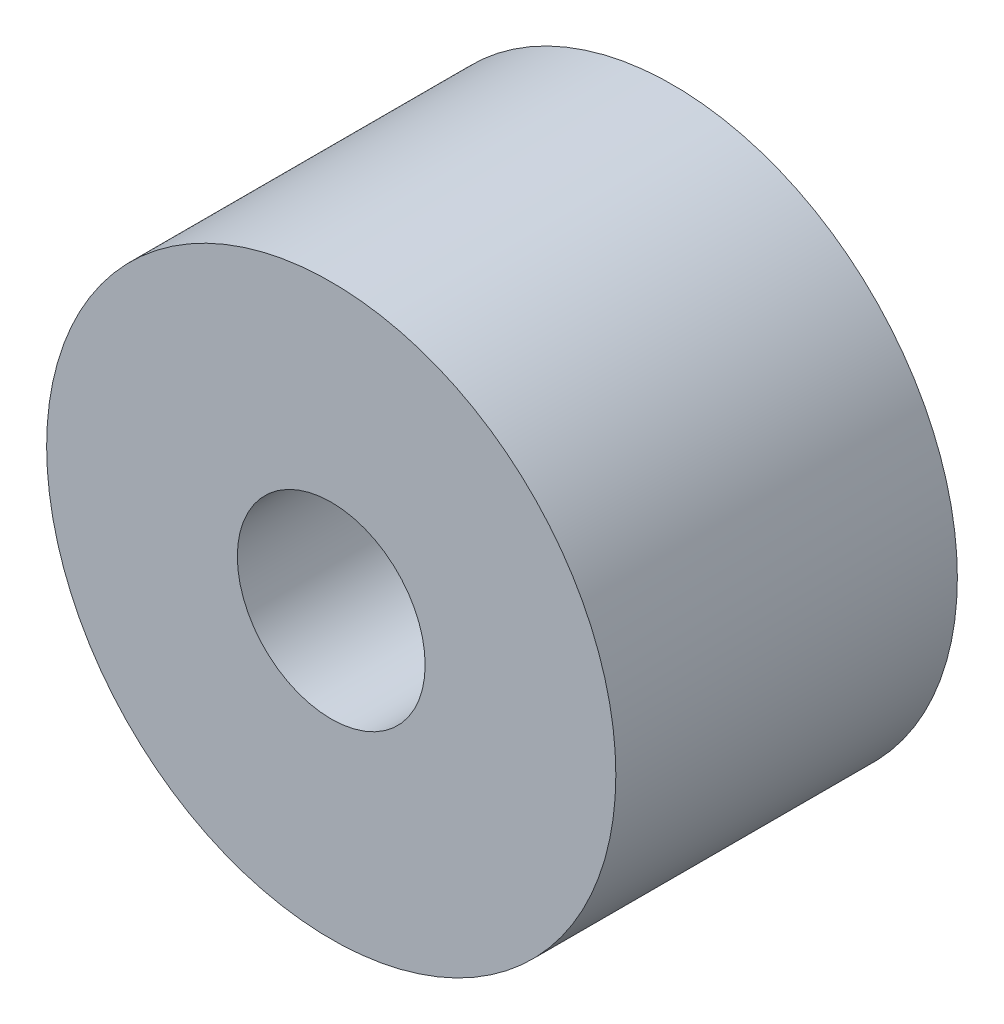
SolidWorks part; units mm, degrees
ref_plane "正面" through (0, 0, 0) normal (0, 0, 1) x (1, 0, 0)
ref_plane "平面" through (0, 0, 0) normal (0, 1, 0) x (1, 0, 0)
ref_plane "右側面" through (0, 0, 0) normal (1, 0, 0) x (0, 0, -1)
sketch "ｽｹｯﾁ1" plane through (0, 0, 0) normal (0, 0, 1) x (1, 0, 0)
  line L0 (-40.4809, 47.4644) -> (-19.4119, 52.6725)
  line L1 (-19.4119, 52.6725) -> (-14.914, 47.4644)
  line L2 (-14.914, 47.4644) -> (-13.1226, 40.2175)
  line L3 (-13.1226, 40.2175) -> (-17.1629, 36.7281)
  line L4 (-17.1629, 36.7281) -> (-17.1629, 28.526)
  line L5 (-17.1629, 28.526) -> (-59.8927, 30.4198)
  line L6 (-59.8927, 30.4198) -> (-61.4521, 36.7281)
  line L7 (-61.4521, 36.7281) -> (-59.8927, 43.8409)
  line L8 (-59.8927, 43.8409) -> (-55.6603, 63.1468)
  line L9 (-55.6603, 63.1468) -> (-57.7765, 63.1468)
  line L10 (-57.7765, 63.1468) -> (-57.7765, 69.4803)
  line L11 (-57.7765, 69.4803) -> (-60.6724, 72.8334)
  line L12 (-60.6724, 72.8334) -> (-67.0927, 74.241)
  line L13 (-67.0927, 74.241) -> (-71.2558, 74.241)
  line L14 (-71.2558, 74.241) -> (-74.357, 74.9208)
  line L15 (-74.357, 74.9208) -> (-67.0927, 78.476)
  line L16 (-67.0927, 78.476) -> (-60.6724, 78.476)
  line L17 (-60.6724, 78.476) -> (-55.6603, 74.241)
  line L18 (-55.6603, 74.241) -> (-47.0998, 74.241)
  line L19 (-47.0998, 74.241) -> (-41.4656, 69.4803)
  line L20 (-41.4656, 69.4803) -> (-40.4809, 53.4938)
  line L21 (-40.4809, 53.4938) -> (-40.4809, 47.4644)
  line L22 (103.0358, 67.5865) -> (103.0358, 78.476)
  line L23 (103.0358, 78.476) -> (111.9152, 78.476)
  line L24 (111.9152, 78.476) -> (111.9152, 67.5865)
  line L25 (111.9152, 67.5865) -> (122.8047, 67.5865)
  line L26 (122.8047, 67.5865) -> (122.8047, 58.7071)
  line L27 (122.8047, 58.7071) -> (111.9152, 58.7071)
  line L28 (111.9152, 58.7071) -> (111.9152, 47.8175)
  line L29 (111.9152, 47.8175) -> (103.0358, 47.8175)
  line L30 (103.0358, 47.8175) -> (103.0358, 58.7071)
  line L31 (103.0358, 58.7071) -> (92.1462, 58.7071)
  line L32 (92.1462, 58.7071) -> (92.1462, 67.5865)
  line L33 (92.1462, 67.5865) -> (103.0358, 67.5865)
  line L34 (41.6645, 50.0684) -> (33.8524, 36.7281)
  line L35 (33.8524, 36.7281) -> (30.8018, 38.5145)
  line L36 (30.8018, 38.5145) -> (25.686, 29.7785)
  line L37 (25.686, 29.7785) -> (20.5955, 28.526)
  line L38 (20.5955, 28.526) -> (17.9766, 24.0538)
  line L39 (17.9766, 24.0538) -> (14.8342, 18.6876)
  line L40 (14.8342, 18.6876) -> (14.8342, 13.612)
  line L41 (14.8342, 13.612) -> (17.9766, 5.5632)
  line L42 (17.9766, 5.5632) -> (21.1614, -2.5939)
  line L43 (21.1614, -2.5939) -> (19.569, -10.2978)
  line L44 (19.569, -10.2978) -> (16.4054, -15.7001)
  line L45 (16.4054, -15.7001) -> (10.482, -18.0127)
  line L46 (10.482, -18.0127) -> (-0.7783, -22.409)
  line L47 (-0.7783, -22.409) -> (-11.1263, -22.409)
  line L48 (-11.1263, -22.409) -> (-24.8567, -18.0127)
  line L49 (-24.8567, -18.0127) -> (-29.5913, -10.2978)
  line L50 (-29.5913, -10.2978) -> (-32.1251, 0)
  line L51 (-32.1251, 0) -> (-108.9262, -34.7071)
  line L52 (-108.9262, -34.7071) -> (-108.9262, -38.2319)
  line L53 (-108.9262, -38.2319) -> (-103.9245, -38.2319)
  line L54 (-103.9245, -38.2319) -> (-102.0442, -41.2959)
  line L55 (-102.0442, -41.2959) -> (-97.7591, -42.668)
  line L56 (-97.7591, -42.668) -> (-95.736, -50.8902)
  line L57 (-95.736, -50.8902) -> (-92.0846, -56.84)
  line L58 (-92.0846, -56.84) -> (-84.2874, -59.3366)
  line L59 (-84.2874, -59.3366) -> (-74.357, -59.3366)
  line L60 (-74.357, -59.3366) -> (-30.8582, -39.6791)
  line L61 (-30.8582, -39.6791) -> (-27.224, -38.0368)
  line L62 (-27.224, -38.0368) -> (-22.8371, -35.3446)
  line L63 (-22.8371, -35.3446) -> (-11.1263, -35.3446)
  line L64 (-11.1263, -35.3446) -> (-0.7783, -35.3446)
  line L65 (-0.7783, -35.3446) -> (10.482, -30.256)
  line L66 (10.482, -30.256) -> (21.7814, -23.3216)
  line L67 (21.7814, -23.3216) -> (30.8018, -12.9989)
  line L68 (30.8018, -12.9989) -> (35.969, -4.1751)
  line L69 (35.969, -4.1751) -> (40.5416, 3.6333)
  line L70 (40.5416, 3.6333) -> (40.5416, 9.5876)
  line L71 (40.5416, 9.5876) -> (45.1164, 17.3997)
  line L72 (45.1164, 17.3997) -> (47.4419, 21.3707)
  line L73 (47.4419, 21.3707) -> (45.1164, 30.8218)
  line L74 (45.1164, 30.8218) -> (41.6645, 33.8381)
  line L75 (41.6645, 33.8381) -> (49.8508, 47.8175)
  line L76 (49.8508, 47.8175) -> (41.6645, 50.0684)
  line L77 (77.2935, 67.6446) -> (77.2935, 32.33)
  line L78 (77.2935, 32.33) -> (77.2935, 28.526)
  line L79 (77.2935, 28.526) -> (82.4095, 27.1193)
  line L80 (82.4095, 27.1193) -> (87.6627, 25.6749)
  line L81 (87.6627, 25.6749) -> (92.1462, 25.6749)
  line L82 (92.1462, 25.6749) -> (120.0222, 21.3707)
  line L83 (120.0222, 21.3707) -> (127.0357, 25.6749)
  line L84 (127.0357, 25.6749) -> (131.2042, 52.6725)
  line L85 (122.8047, 58.7071) -> (131.2042, 58.7071)
  line L86 (131.2042, 58.7071) -> (131.2042, 52.6725)
  line L87 (120.0222, 58.7071) -> (120.0222, 55.1166)
  line L88 (120.0222, 55.1166) -> (120.0222, 43.3983)
  line L89 (120.0222, 43.3983) -> (90.3217, 43.9227)
  line L90 (90.3217, 43.9227) -> (87.52, 48.488)
  line L91 (87.52, 48.488) -> (90.3217, 55.7115)
  line L92 (90.3217, 55.7115) -> (85.0361, 57.7616)
  line L93 (85.0361, 57.7616) -> (85.0361, 67.6446)
  line L94 (85.0361, 67.6446) -> (77.2935, 67.6446)
  line L95 (-17.1629, 67.6446) -> (-17.1629, 60.6019)
  line L96 (-17.1629, 60.6019) -> (19.2861, 54.9741)
  line L97 (19.2861, 54.9741) -> (19.2861, 43.3983)
  line L98 (19.2861, 43.3983) -> (28.2439, 42.0152)
  line L99 (28.2439, 42.0152) -> (33.2702, 54.9741)
  line L100 (33.2702, 54.9741) -> (47.4419, 54.9741)
  line L101 (47.4419, 54.9741) -> (49.8508, 40.8278)
  line L102 (49.8508, 40.8278) -> (61.8287, 38.9784)
  line L103 (61.8287, 38.9784) -> (77.2935, 49.9873)
  line L104 (77.2935, 49.9873) -> (77.2935, 74.241)
  line L105 (77.2935, 74.241) -> (52.7136, 74.241)
  line L106 (52.7136, 74.241) -> (49.8508, 74.241)
  line L107 (49.8508, 74.241) -> (10.482, 74.9361)
  line L108 (10.482, 74.9361) -> (-11.1263, 69.6193)
  line L109 (-11.1263, 69.6193) -> (-17.1629, 67.6446)
  line L110 (-17.1629, 36.7281) -> (-11.1263, 41.9415)
  line L111 (-11.1263, 41.9415) -> (-5.9183, 40.7998)
  line L112 (-5.9183, 40.7998) -> (-2.4018, 36.7281)
  line L113 (-2.4018, 36.7281) -> (-4.16, 35.2096)
  line L114 (-4.16, 35.2096) -> (-4.16, 32.627)
  line L115 (-4.16, 32.627) -> (2.7481, 34.3347)
  line L116 (2.7481, 34.3347) -> (6.683, 29.7785)
  line L117 (6.683, 29.7785) -> (8.0981, 24.0538)
  line L118 (8.0981, 24.0538) -> (8.0981, 18.6876)
  line L119 (8.0981, 18.6876) -> (7.3906, 15.4602)
  line L120 (7.3906, 15.4602) -> (0, 15.4602)
  line L121 (0, 15.4602) -> (-11.1263, 7.5398)
  line L122 (-11.1263, 7.5398) -> (-15.1428, 2.7864)
  line L123 (-15.1428, 2.7864) -> (-16.8824, -5.1489)
  line L124 (-16.8824, -5.1489) -> (-14.321, -8.7471)
  line L125 (-14.321, -8.7471) -> (-12.9841, -14.1552)
  line L126 (-12.9841, -14.1552) -> (-12.9841, -16.8564)
  line L127 (-12.9841, -16.8564) -> (-14.321, -16.8564)
  line L128 (-14.321, -16.8564) -> (-17.4929, -12.4005)
  line L129 (-17.4929, -12.4005) -> (-20.7137, -7.8762)
  line L130 (-20.7137, -7.8762) -> (-20.7137, 0)
  line L131 (-20.7137, 0) -> (-20.7137, 5.1631)
  line L132 (-20.7137, 5.1631) -> (-14.5919, 12.4081)
  line L133 (-14.5919, 12.4081) -> (-14.5919, 21.3707)
  line L134 (-14.5919, 21.3707) -> (-14.5919, 28.526)
  line L135 (-14.5919, 28.526) -> (-17.1629, 36.7281)
  line L136 (-29.9464, 29.0926) -> (-29.9464, 24.0538)
  line L137 (-29.9464, 24.0538) -> (-27.224, 21.7535)
  line L138 (-27.224, 21.7535) -> (-24.8567, 22.4956)
  line L139 (-24.8567, 22.4956) -> (-20.7137, 18.9949)
  line L140 (-20.7137, 18.9949) -> (-27.224, 14.3604)
  line L141 (-27.224, 14.3604) -> (-34.9273, 14.3604)
  line L142 (-34.9273, 14.3604) -> (-40.4809, 14.3604)
  line L143 (-40.4809, 14.3604) -> (-51.38, 16.7498)
  line L144 (-51.38, 16.7498) -> (-55.6603, 22.7625)
  line L145 (-55.6603, 22.7625) -> (-59.8927, 30.4198)
  line L146 (-203.8246, 40.2175) -> (-178.0211, 40.2175)
  line L147 (-178.0211, 40.2175) -> (-154.8215, 28.526)
  line L148 (-154.8215, 28.526) -> (-144.6421, 25.6749)
  line L149 (-144.6421, 25.6749) -> (-126.4139, 27.1004)
  line L150 (-126.4139, 27.1004) -> (-95.736, 36.7281)
  line L151 (-95.736, 36.7281) -> (-67.0927, 45.7172)
  line L152 (-67.0927, 45.7172) -> (-68.8885, 29.0926)
  line L153 (-68.8885, 29.0926) -> (-170.9524, -4.2036)
  line L154 (-170.9524, -4.2036) -> (-170.9524, -19.0928)
  line L155 (-170.9524, -19.0928) -> (-124.3581, -4.4701)
  line L156 (-124.3581, -4.4701) -> (-84.2874, -1.3363)
  line L157 (-84.2874, -1.3363) -> (-83.0909, -5.1489)
  line L158 (-83.0909, -5.1489) -> (-201.4573, -43.7634)
  line L159 (-83.0909, -5.1489) -> (-20.7137, 14.427)
  line L160 (-20.7137, 14.427) -> (-11.1263, 14.427)
  line L161 (-11.1263, 14.427) -> (14.8342, 7.1558)
  line L162 (14.8342, 7.1558) -> (38.587, 4.5901)
  line L163 (38.587, 4.5901) -> (41.6645, 11.505)
  line L164 (41.6645, 11.505) -> (52.7136, 18.6876)
  line L165 (52.7136, 18.6876) -> (139.0451, 9.3623)
  line L166 (139.0451, 9.3623) -> (157.8816, 41.5283)
  line L167 (157.8816, 41.5283) -> (192.976, 41.5283)
  line L168 (-67.0927, 45.7172) -> (-20.7137, 60.6019)
  line L169 (-20.7137, 60.6019) -> (-17.1629, 67.6446)
  line L170 (77.2935, 71.1374) -> (141.5646, 67.1712)
  line L171 (141.5646, 67.1712) -> (185.8331, 67.1712)
  line L172 (-84.2874, -31.1596) -> (-44.5413, -13.946)
  line L173 (-75.2823, -51.2258) -> (-36.0851, -32.5448)
  line L174 (-17.1629, 67.6446) -> (77.2935, 67.6446)
  line L175 (-201.4573, -43.7634) -> (-231.4344, -53.5428)
  line L176 (-231.4344, -53.5428) -> (-231.4344, 16.7498)
  line L177 (-231.4344, 16.7498) -> (-231.4344, 32.627)
  line L178 (-231.4344, 32.627) -> (-225.6893, 40.2175)
  line L179 (-225.6893, 40.2175) -> (-203.8246, 40.2175)
  line L180 (-203.8246, 40.2175) -> (-202.2074, 40.2551)
  line L181 (192.976, 41.5283) -> (252.9726, 41.5283)
  line L182 (252.9726, 41.5283) -> (276.2364, 47.8175)
  line L183 (276.2364, 47.8175) -> (276.2364, 51.3763)
  line L184 (276.2364, 51.3763) -> (333.0358, 51.3763)
  line L185 (333.0358, 51.3763) -> (333.0358, 67.1712)
  line L186 (333.0358, 67.1712) -> (185.8331, 67.1712)
  line L187 (333.0358, 67.5865) -> (436.0426, 67.5865)
  line L188 (436.0426, 67.5865) -> (436.0426, 51.3763)
  line L189 (157.8816, 41.5283) -> (157.8816, 67.1712)
  line L190 (52.7136, 18.6876) -> (57.0922, 28.526)
  line L191 (57.0922, 28.526) -> (127.0357, 18.6876)
  line L192 (127.0357, 18.6876) -> (134.8969, 23.7979)
  line L193 (134.8969, 23.7979) -> (142.7878, 41.5283)
  line L194 (142.7878, 41.5283) -> (157.8816, 41.5283)
  circle A0 centre (-37.6401, 36.7281) radius 1.65
  circle A1 centre (-5.9183, 21.8975) radius 1.65
  circle A2 centre (26.5138, 17.3997) radius 1.65
  circle A3 centre (38.587, 28.526) radius 1.65
  circle A4 centre (107.4755, 63.1468) radius 1.65
  circle A5 centre (116.9447, 27.1193) radius 1.65
  arc A6 (-84.2874, -31.1596) -> (-75.2823, -51.2258) centre (-80.0148, -41.2959) ccw
  arc A7 (-36.0851, -32.5448) -> (-44.5413, -13.946) centre (-40.4809, -23.3216) ccw
  circle A8 centre (-156.3143, -7.8762) radius 1.65
  point P51 (107.4755, 63.1468)
  point P190 (-31.1799, -19.0928)
  point P192 (-90.0505, -45.7997)
  dimension "D1" = 4
  dimension "D2" = 11
  dimension "D3" = 230
  dimension "D4" = 564.4702
  dimension "D6" = 3.3
  dimension "D5" = 389.316
extrude "ﾎﾞｽ - 押し出し1" add sketch "ｽｹｯﾁ1" along normal mid plane 6 contours L170 L22 L33 L32 L31 L30 L29 L28 L27 L26 L25 L24 A4 | L22 L170 L24 L23 | L65 L66 L67 L68 L69 L70 L71 L72 L73 L74 L75 L76 L34 L35 L36 L37 L38 L39 L40 L41 L42 L43 L44 L45 L46 L47 L48 L49 L50 L51 L52 L53 L54 L55 L56 L57 L58 L59 L60 L61 L62 L63 L64
fillet "ﾌｨﾚｯﾄ1" radius 4 4 edges at (111.9152, 47.8175, 0) (92.1462, 58.7071, 0) (103.0358, 78.476, 0) (122.8047, 67.5865, 0)
fillet "ﾌｨﾚｯﾄ2" radius 2 4 edges at (111.9152, 67.5865, 0) (111.9152, 58.7071, 0) (103.0358, 58.7071, 0) (103.0358, 67.5865, 0)
sketch "ｽｹｯﾁ2" plane through (0, 0, 3) normal (0, 0, 1) x (1, 0, 0)
  circle A0 centre (107.4755, 63.1468) radius 1.65
  circle A1 centre (107.4755, 63.1468) radius 5
  circle A3 centre (107.4755, 63.1468) radius 32.3837
  line M2 (103.0358, 47.8175) -> (107.9152, 47.8175)
  arc M3 (107.9152, 47.8175) -> (111.9152, 51.8175) centre (107.9152, 51.8175) ccw
  line M4 (111.9152, 51.8175) -> (111.9152, 56.7071)
  arc M5 (111.9152, 56.7071) -> (113.9152, 58.7071) centre (113.9152, 56.7071) cw
  line M6 (113.9152, 58.7071) -> (122.8047, 58.7071)
  line M7 (122.8047, 58.7071) -> (122.8047, 63.5865)
  arc M8 (122.8047, 63.5865) -> (118.8047, 67.5865) centre (118.8047, 63.5865) ccw
  line M9 (118.8047, 67.5865) -> (113.9152, 67.5865)
  arc M10 (113.9152, 67.5865) -> (111.9152, 69.5865) centre (113.9152, 69.5865) cw
  line M11 (111.9152, 69.5865) -> (111.9152, 78.476)
  line M12 (111.9152, 78.476) -> (107.0358, 78.476)
  arc M13 (107.0358, 78.476) -> (103.0358, 74.476) centre (107.0358, 74.476) ccw
  line M14 (103.0358, 74.476) -> (103.0358, 69.5865)
  arc M15 (103.0358, 69.5865) -> (101.0358, 67.5865) centre (101.0358, 69.5865) cw
  line M16 (101.0358, 67.5865) -> (92.1462, 67.5865)
  line M17 (92.1462, 67.5865) -> (92.1462, 62.7071)
  arc M18 (92.1462, 62.7071) -> (96.1462, 58.7071) centre (96.1462, 62.7071) ccw
  line M19 (96.1462, 58.7071) -> (101.0358, 58.7071)
  arc M20 (101.0358, 58.7071) -> (103.0358, 56.7071) centre (101.0358, 56.7071) cw
  line M21 (103.0358, 56.7071) -> (103.0358, 47.8175)
  dimension "D1" = 10
extrude "ｶｯﾄ - 押し出し1" cut sketch "ｽｹｯﾁ2" against normal blind 10 contours A1 M21 M2 M3 M4 M5 M6 M7 M8 M9 M10 M11 M12 M13 M14 M15 M16 M17 M18 M19 M20 | A3 M2 M21 M20 M19 M18 M17 M16 M15 M14 M13 M12 M11 M10 M9 M8 M7 M6 M5 M4 M3
